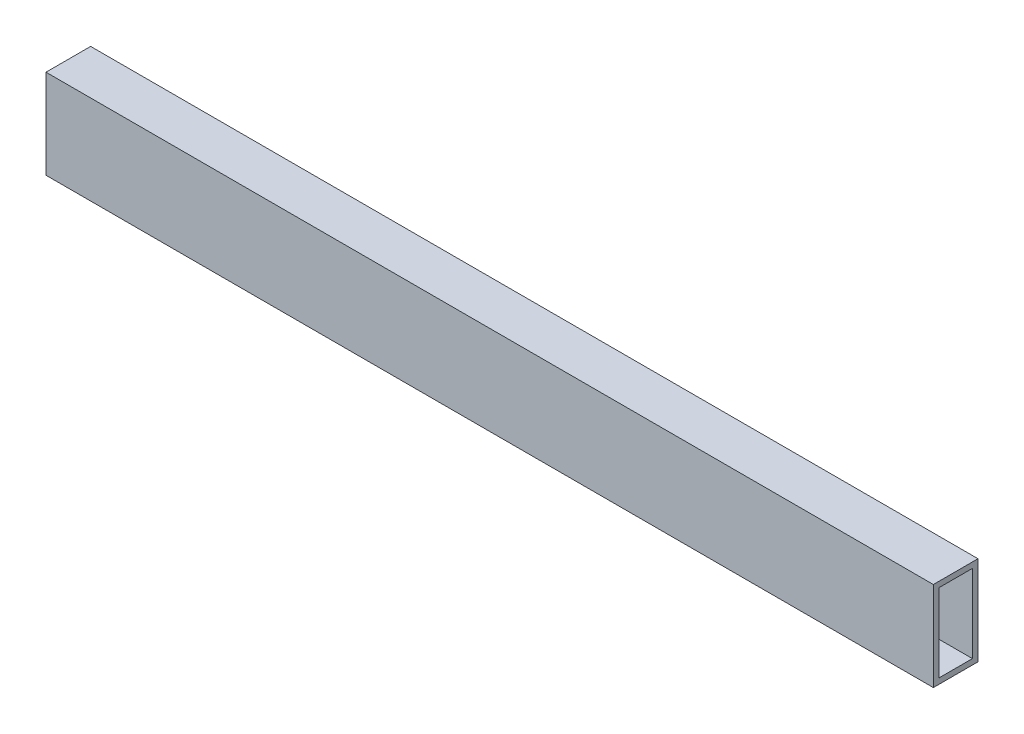
SolidWorks part; units mm, degrees
ref_plane "Front Plane" through (0, 0, 0) normal (0, 0, 1) x (1, 0, 0)
ref_plane "Top Plane" through (0, 0, 0) normal (0, 1, 0) x (1, 0, 0)
ref_plane "Right Plane" through (0, 0, 0) normal (1, 0, 0) x (0, 0, -1)
sketch "Sketch1" plane through (0, 0, 0) normal (1, 0, 0) x (0, 0, -1)
  line L1 (0, 0) -> (25.4, 0)
  line L2 (0, 0) -> (0, 50.8)
  line L3 (0, 50.8) -> (25.4, 50.8)
  line L4 (25.4, 0) -> (25.4, 50.8)
  line L5 (3.175, 47.625) -> (22.225, 47.625)
  line L6 (3.175, 47.625) -> (3.175, 3.175)
  line L7 (3.175, 3.175) -> (22.225, 3.175)
  line L8 (22.225, 47.625) -> (22.225, 3.175)
  dimension "D1" = 3.175
  dimension "D2" = 3.175
  dimension "D3" = 3.175
  dimension "D4" = 3.175
  dimension "D5" = 25.4
  dimension "D6" = 50.8
extrude "Boss-Extrude1" add sketch "Sketch1" along normal blind 504.825
